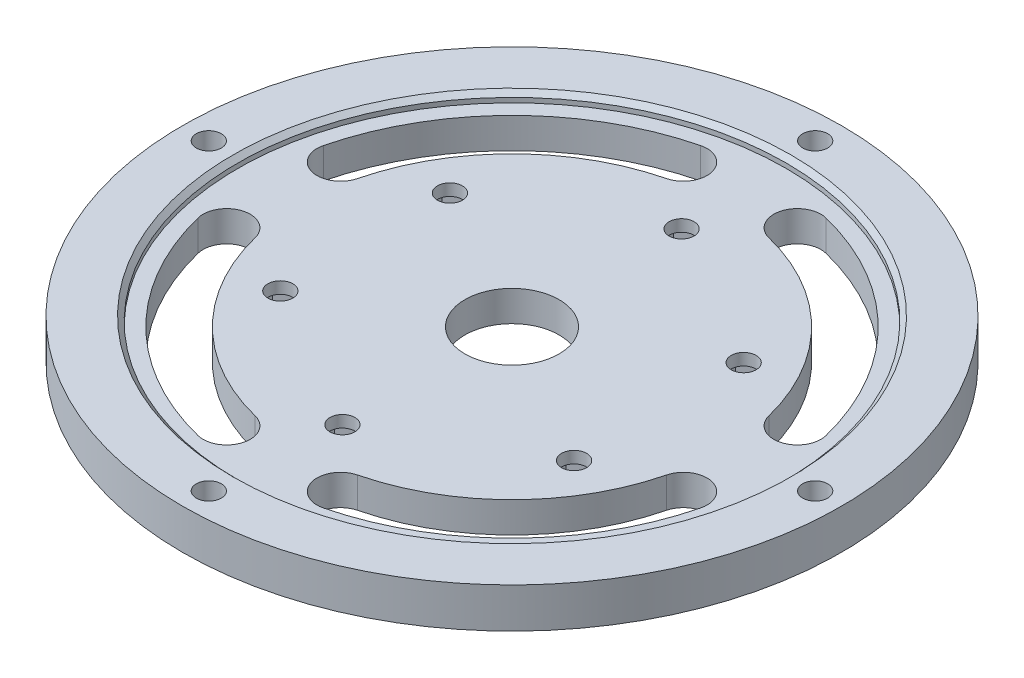
SolidWorks part; units mm, degrees
ref_plane "Front Plane" through (0, 0, 0) normal (0, 0, 1) x (1, 0, 0)
ref_plane "Top Plane" through (0, 0, 0) normal (0, 1, 0) x (1, 0, 0)
ref_plane "Right Plane" through (0, 0, 0) normal (1, 0, 0) x (0, 0, -1)
sketch "Sketch1" plane through (0, 0, 0) normal (0, 1, 0) x (1, 0, 0)
  circle A0 centre (0, 0) radius 70
  dimension "D1" = 140
extrude "Boss-Extrude1" add sketch "Sketch1" along normal blind 6.5
sketch "Sketch2" plane through (0, 6.5, 0) normal (0, 1, 0) x (1, 0, 0)
  line L0 (0, 0) -> (0, 64.4) construction
  line L1 (-9.5984, 70) -> (9.8626, 70) construction
  circle A0 centre (0, 64.4) radius 2.65
  circle A2 centre (0, 0) radius 70 construction
  circle A3 centre (64.4, 0) radius 2.65
  circle A4 centre (0, -64.4) radius 2.65
  circle A5 centre (-64.4, 0) radius 2.65
  point P17 (0, 0)
  dimension "D1" = 5.3
  dimension "D2" = 5.6
  dimension "D3" = 4
extrude "Cut-Extrude1" cut sketch "Sketch2" against normal through all
sketch "Sketch3" plane through (0, 6.5, 0) normal (0, 1, 0) x (1, 0, 0)
  circle A0 centre (0, 0) radius 58.25
  circle A1 centre (0, 0) radius 70 construction
  circle A2 centre (0, 0) radius 70
  circle A3 centre (-64.4, 0) radius 2.65
  circle A4 centre (0, 64.4) radius 2.65
  circle A5 centre (64.4, 0) radius 2.65
  circle A6 centre (0, -64.4) radius 2.65
  circle A7 centre (-64.4, 0) radius 2.65 construction
  dimension "D1" = 11.75
extrude "Boss-Extrude2" add sketch "Sketch3" along normal blind 2
sketch "Sketch4" plane through (0, 6.5, 0) normal (0, 1, 0) x (1, 0, 0)
  line L0 (0, 0) -> (-35.3553, 35.3553) construction
  line L1 (-12.0961, 48.5148) -> (0, 0) construction
  line L2 (0, 0) -> (-48.5148, 12.0961) construction
  line L4 (0, 64.4) -> (0, 0) construction
  circle A4 centre (0, 0) radius 50 construction
  circle A10 centre (0, 64.4) radius 2.65 construction
  arc A11 (-12.0961, 48.5148) -> (-48.5148, 12.0961) centre (0, 0) ccw construction
  arc A12 (-13.3057, 53.3663) -> (-53.3663, 13.3057) centre (0, 0) ccw
  arc A13 (-10.8865, 43.6633) -> (-43.6633, 10.8865) centre (0, 0) ccw
  arc A14 (-10.8865, 43.6633) -> (-13.3057, 53.3663) centre (-12.0961, 48.5148) ccw
  arc A15 (-53.3663, 13.3057) -> (-43.6633, 10.8865) centre (-48.5148, 12.0961) ccw
  arc A16 (43.6633, 10.8865) -> (10.8865, 43.6633) centre (0, 0) ccw
  arc A17 (43.6633, 10.8865) -> (53.3663, 13.3057) centre (48.5148, 12.0961) ccw
  arc A18 (13.3057, 53.3663) -> (10.8865, 43.6633) centre (12.0961, 48.5148) ccw
  arc A19 (53.3663, 13.3057) -> (13.3057, 53.3663) centre (0, 0) ccw
  arc A20 (48.5148, 12.0961) -> (12.0961, 48.5148) centre (0, 0) ccw construction
  arc A21 (10.8865, -43.6633) -> (43.6633, -10.8865) centre (0, 0) ccw
  arc A22 (10.8865, -43.6633) -> (13.3057, -53.3663) centre (12.0961, -48.5148) ccw
  arc A23 (53.3663, -13.3057) -> (43.6633, -10.8865) centre (48.5148, -12.0961) ccw
  arc A24 (13.3057, -53.3663) -> (53.3663, -13.3057) centre (0, 0) ccw
  arc A25 (12.0961, -48.5148) -> (48.5148, -12.0961) centre (0, 0) ccw construction
  arc A26 (-43.6633, -10.8865) -> (-10.8865, -43.6633) centre (0, 0) ccw
  arc A27 (-43.6633, -10.8865) -> (-53.3663, -13.3057) centre (-48.5148, -12.0961) ccw
  arc A28 (-13.3057, -53.3663) -> (-10.8865, -43.6633) centre (-12.0961, -48.5148) ccw
  arc A29 (-53.3663, -13.3057) -> (-13.3057, -53.3663) centre (0, 0) ccw
  arc A30 (-48.5148, -12.0961) -> (-12.0961, -48.5148) centre (0, 0) ccw construction
  point P8 (-35.3553, 35.3553)
  point P22 (35.3553, 35.3553)
  point P29 (35.3553, -35.3553)
  point P36 (-35.3553, -35.3553)
  point P41 (0, 0)
  dimension "D1" = 100
  dimension "D2" = 45
  dimension "D4" = 10
  dimension "D3" = 62
  dimension "D5" = 4
extrude "Cut-Extrude2" cut sketch "Sketch4" against normal through all
sketch "Sketch5" plane through (0, 6.5, 0) normal (0, 1, 0) x (1, 0, 0)
  line L0 (0, 0) -> (0, 36.0215) construction
  circle A0 centre (0, 36.0215) radius 2.65
  circle A1 centre (31.1955, 18.0107) radius 2.65
  circle A2 centre (31.1955, -18.0107) radius 2.65
  circle A3 centre (0, -36.0215) radius 2.65
  circle A4 centre (-31.1955, -18.0107) radius 2.65
  circle A5 centre (-31.1955, 18.0107) radius 2.65
  point P17 (0, 0)
  dimension "D2" = 5.3
  dimension "D1" = 36.0215
  dimension "D3" = 6
extrude "Cut-Extrude3" cut sketch "Sketch5" against normal through all
sketch "Sketch6" plane through (0, 0, 0) normal (0, -1, 0) x (1, 0, 0)
  line L0 (0, 0) -> (35.1955, -20.3201) construction
  line L1 (27.1955, -20.3201) -> (31.1955, -22.6295)
  line L2 (31.1955, -22.6295) -> (35.1955, -20.3201)
  line L3 (35.1955, -20.3201) -> (35.1955, -15.7013)
  line L4 (35.1955, -15.7013) -> (31.1955, -13.3919)
  line L5 (31.1955, -13.3919) -> (27.1955, -15.7013)
  line L6 (27.1955, -15.7013) -> (27.1955, -20.3201)
  line L7 (-4, -33.7121) -> (-4, -38.3309)
  line L8 (-4, -38.3309) -> (0, -40.6403)
  line L9 (0, -40.6403) -> (4, -38.3309)
  line L10 (4, -38.3309) -> (4, -33.7121)
  line L11 (4, -33.7121) -> (0, -31.4027)
  line L12 (0, -31.4027) -> (-4, -33.7121)
  line L13 (-31.1955, -13.3919) -> (-35.1955, -15.7013)
  line L14 (-35.1955, -15.7013) -> (-35.1955, -20.3201)
  line L15 (-35.1955, -20.3201) -> (-31.1955, -22.6295)
  line L16 (-31.1955, -22.6295) -> (-27.1955, -20.3201)
  line L17 (-27.1955, -20.3201) -> (-27.1955, -15.7013)
  line L18 (-27.1955, -15.7013) -> (-31.1955, -13.3919)
  line L19 (-27.1955, 20.3201) -> (-31.1955, 22.6295)
  line L20 (-31.1955, 22.6295) -> (-35.1955, 20.3201)
  line L21 (-35.1955, 20.3201) -> (-35.1955, 15.7013)
  line L22 (-35.1955, 15.7013) -> (-31.1955, 13.3919)
  line L23 (-31.1955, 13.3919) -> (-27.1955, 15.7013)
  line L24 (-27.1955, 15.7013) -> (-27.1955, 20.3201)
  line L25 (4, 33.7121) -> (4, 38.3309)
  line L26 (4, 38.3309) -> (0, 40.6403)
  line L27 (0, 40.6403) -> (-4, 38.3309)
  line L28 (-4, 38.3309) -> (-4, 33.7121)
  line L29 (-4, 33.7121) -> (0, 31.4027)
  line L30 (0, 31.4027) -> (4, 33.7121)
  line L31 (31.1955, 13.3919) -> (35.1955, 15.7013)
  line L32 (35.1955, 15.7013) -> (35.1955, 20.3201)
  line L33 (35.1955, 20.3201) -> (31.1955, 22.6295)
  line L34 (31.1955, 22.6295) -> (27.1955, 20.3201)
  line L35 (27.1955, 20.3201) -> (27.1955, 15.7013)
  line L36 (27.1955, 15.7013) -> (31.1955, 13.3919)
  circle A0 centre (31.1955, -18.0107) radius 4 construction
  point P44 (0, 0)
  dimension "D1" = 8
  dimension "D2" = 6
extrude "Cut-Extrude4" cut sketch "Sketch6" against normal blind 4
sketch "Sketch7" plane through (0, 6.5, 0) normal (0, 1, 0) x (1, 0, 0)
  circle A0 centre (0, 0) radius 10
  dimension "D1" = 20
extrude "Cut-Extrude5" cut sketch "Sketch7" against normal through all
chamfer "Chamfer1" distance 1 angle 45 1 edges at (0, 8.5, 58.25)
sketch "Sketch8" plane through (0, 0, 0) normal (0, -1, 0) x (1, 0, 0)
  circle A0 centre (-64.4, 0) radius 4.35
  circle A1 centre (0, 64.4) radius 4.35
  circle A2 centre (64.4, 0) radius 4.35
  circle A3 centre (0, -64.4) radius 4.35
  dimension "D1" = 8.7
extrude "Cut-Extrude6" cut sketch "Sketch8" against normal blind 4
